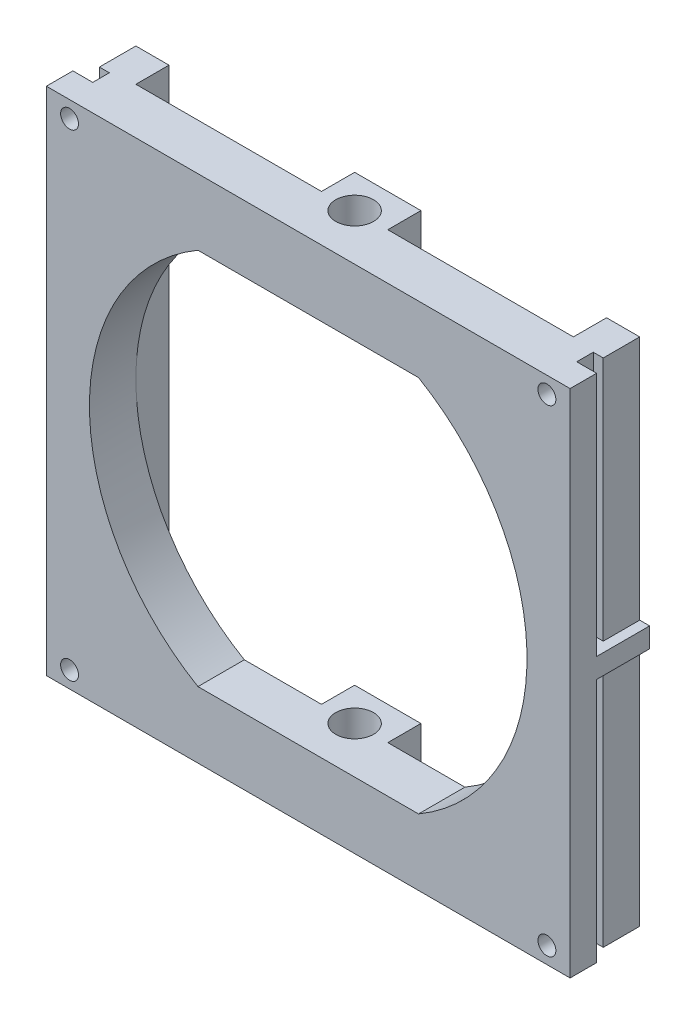
SolidWorks part; units mm, degrees
ref_plane "Front Plane" through (0, 0, 0) normal (0, 0, 1) x (1, 0, 0)
ref_plane "Top Plane" through (0, 0, 0) normal (0, 1, 0) x (1, 0, 0)
ref_plane "Right Plane" through (0, 0, 0) normal (1, 0, 0) x (0, 0, -1)
sketch "Sketch1" plane through (0, 0, 0) normal (0, 0, 1) x (1, 0, 0)
  line L1 (0, 0) -> (79, 0)
  line L2 (0, 0) -> (0, 77)
  line L3 (0, 77) -> (79, 77)
  line L4 (79, 0) -> (79, 77)
  line L6 (22.8642, 67) -> (56.1358, 67)
  line L12 (22.8642, 10) -> (56.1358, 10)
  arc A2 (22.8642, 67) -> (22.8642, 10) centre (39.5, 38.5) ccw
  arc A3 (56.1358, 10) -> (56.1358, 67) centre (39.5, 38.5) ccw
extrude "Boss-Extrude1" add sketch "Sketch1" along normal blind 12
sketch "Sketch3" plane through (0, 0, 0) normal (0, -1, 0) x (1, 0, 0)
  line L2 (0, 0) -> (1.5, 0)
  line L3 (0, 0) -> (0, 8)
  line L5 (1.5, 0) -> (1.5, 5.5)
  line L6 (79, 0) -> (77.5, 0)
  line L7 (79, 0) -> (79, 8)
  line L9 (77.5, 0) -> (77.5, 5.5)
  line L10 (76, 8) -> (79, 8)
  line L13 (1.5, 5.5) -> (3, 5.5)
  line L14 (3, 8) -> (3, 5.5)
  line L17 (77.5, 5.5) -> (76, 5.5)
  line L18 (76, 8) -> (76, 5.5)
  line L19 (0, 8) -> (3, 8)
extrude "Cut-Extrude1" cut sketch "Sketch3" against normal blind 37
sketch "Sketch4" plane through (0, 77, 0) normal (0, 1, 0) x (1, 0, 0)
  line L6 (76, -8) -> (79, -8)
  line L12 (0, -8) -> (3, -8)
  line L13 (76, -8) -> (76, -5.5)
  line L14 (77.5, -5.5) -> (76, -5.5)
  line L15 (3, -8) -> (3, -5.5)
  line L16 (1.5, -5.5) -> (3, -5.5)
  line L17 (77.5, 0) -> (77.5, -5.5)
  line L18 (79, 0) -> (79, -8)
  line L19 (79, 0) -> (77.5, 0)
  line L20 (1.5, 0) -> (1.5, -5.5)
  line L21 (0, 0) -> (0, -8)
  line L22 (0, 0) -> (1.5, 0)
extrude "Cut-Extrude2" cut sketch "Sketch4" against normal blind 37
sketch "Sketch5" plane through (0, 77, 0) normal (0, 1, 0) x (1, 0, 0)
  line L5 (72.5, -5) -> (44.5, -5)
  line L6 (72.5, -5) -> (72.5, 0)
  line L7 (72.5, 0) -> (44.5, 0)
  line L8 (44.5, -5) -> (44.5, 0)
  line L9 (34.5, 0) -> (6.5, 0)
  line L10 (34.5, 0) -> (34.5, -5)
  line L11 (34.5, -5) -> (6.5, -5)
  line L12 (6.5, 0) -> (6.5, -5)
extrude "Cut-Extrude3" cut sketch "Sketch5" against normal up to surface (77 mm away) up to face at (39.5, 0, 6.5)
sketch "Sketch7" plane through (0, 0, 0) normal (0, -1, 0) x (1, 0, 0)
  circle A0 centre (39.5, 5) radius 2.85
extrude "Cut-Extrude5" cut sketch "Sketch7" against normal up to surface (77 mm away) up to face at (39.5, 77, 4.9)
sketch "Sketch8" plane through (0, 0, 12) normal (0, 0, 1) x (1, 0, 0)
  circle A0 centre (75.5, 2.5) radius 1.35
  circle A1 centre (75.5, 74.5) radius 1.35
  circle A2 centre (3.5, 74.5) radius 1.35
  circle A3 centre (3.5, 2.5) radius 1.35
extrude "Cut-Extrude6" cut sketch "Sketch8" against normal up to surface (4 mm away) up to face at (77.5, 18.5, 8)
